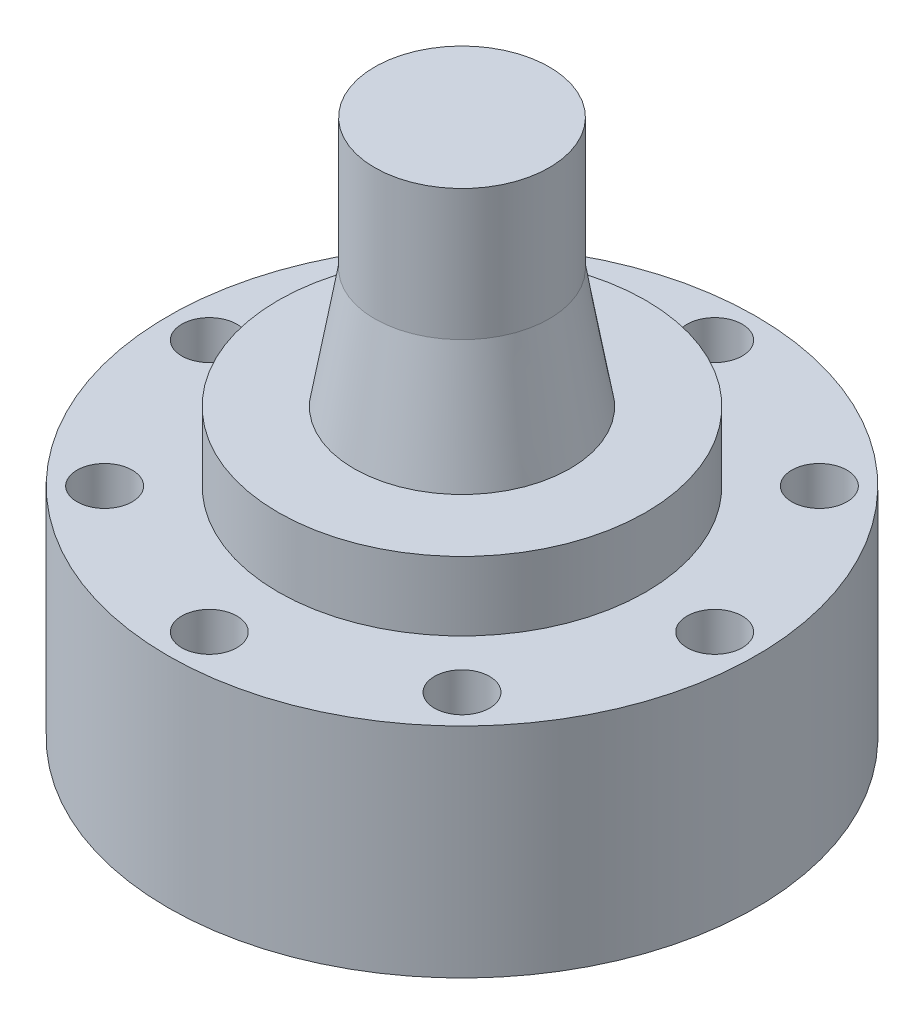
SolidWorks part; units mm, degrees
ref_plane "정면" through (0, 0, 0) normal (0, 0, 1) x (1, 0, 0)
ref_plane "윗면" through (0, 0, 0) normal (0, 1, 0) x (1, 0, 0)
ref_plane "우측면" through (0, 0, 0) normal (1, 0, 0) x (0, 0, -1)
sketch "스케치1" plane through (0, 0, 0) normal (0, 1, 0) x (1, 0, 0)
  circle A3 centre (0, 0) radius 12.8
  dimension "D2" = 25.6
extrude "보스-돌출1" add sketch "스케치1" along normal blind 9.5 and the other way blind 3
sketch "스케치18" plane through (0, 0, 0) normal (0, 0, 1) x (1, 0, 0)
  line L0 (0, 15.1882) -> (0, -3.3642) construction
  line L1 (0, 9.5) -> (-4.7, 9.5)
  line L2 (12.8, 9.5) -> (-12.8, 9.5) construction
  line L4 (-3.8, 14.7) -> (-4.7, 9.5)
  line L5 (0, 14.7) -> (0, 9.5)
  line L6 (-3.8, 14.7) -> (-3.8, 20.4)
  line L7 (-3.8, 20.4) -> (0, 20.4)
  line L8 (0, 20.4) -> (0, 14.7)
  dimension "D1" = 4.7
  dimension "D3" = 3.8
revolve "회전1" add sketch "스케치18" angle 360 about L0
ref_plane "평면2" through (0, 20.4, 0) normal (0, 1, 0) x (1, 0, 0)
ref_plane "평면4" through (0, 0, 10) normal (0, 0, 1) x (1, 0, 0)
sketch "스케치24" plane through (0, -3, 0) normal (0, -1, 0) x (1, 0, 0)
  line L0 (-13.754, 0) -> (19.0578, 0) construction
  line L1 (0, 0) -> (0, 11) construction
  line L2 (0, 0) -> (7.7782, 7.7782) construction
  circle A0 centre (0, 11) radius 1.2
  circle A1 centre (0, -11) radius 1.2
  circle A2 centre (7.7782, 7.7782) radius 1.2
  circle A3 centre (11, 0) radius 1.2
  circle A4 centre (7.7782, -7.7782) radius 1.2
  circle A5 centre (0, -11) radius 1.2
  circle A6 centre (-7.7782, -7.7782) radius 1.2
  circle A7 centre (-11, 0) radius 1.2
  circle A8 centre (-7.7782, 7.7782) radius 1.2
  dimension "D2" = 2.4
  dimension "D1" = 11
  dimension "D4" = 45
  dimension "D3" = 8
extrude "컷-돌출1" cut sketch "스케치24" against normal through all contours A0 | A2 | A3 | A1 | A6 | A8 | A4 | A7
sketch "스케치25" plane through (0, -3, 0) normal (0, -1, 0) x (1, 0, 0)
  circle A0 centre (0, 0) radius 5.1
  dimension "D1" = 10.2
extrude "컷-돌출2" cut sketch "스케치25" against normal blind 6
sketch "스케치26" plane through (0, 9.5, 0) normal (0, 1, 0) x (1, 0, 0)
  circle A0 centre (0, 0) radius 8
  circle A1 centre (0, 0) radius 12.8
  dimension "D1" = 16
extrude "컷-돌출4" cut sketch "스케치26" against normal blind 3
